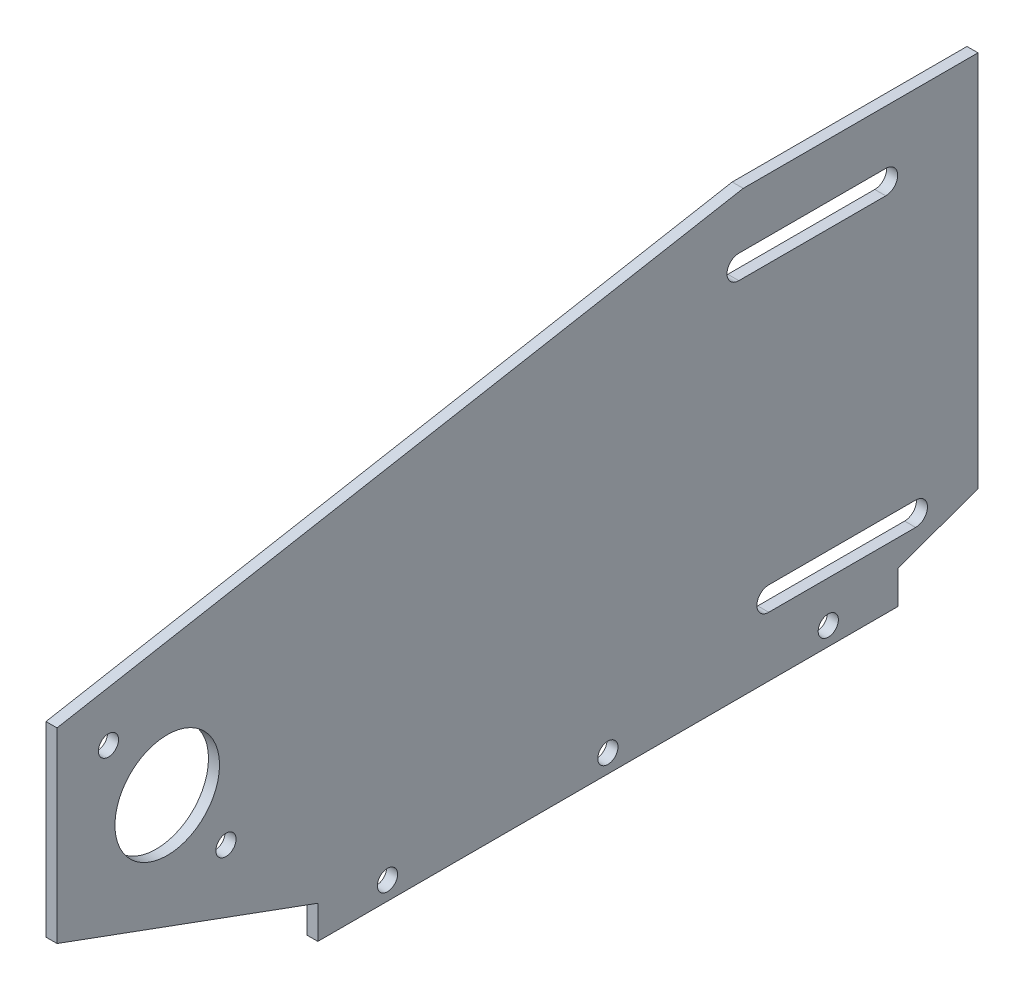
SolidWorks part; units mm, degrees
ref_plane "Front Plane" through (0, 0, 0) normal (0, 0, 1) x (1, 0, 0)
ref_plane "Top Plane" through (0, 0, 0) normal (0, 1, 0) x (1, 0, 0)
ref_plane "Right Plane" through (0, 0, 0) normal (1, 0, 0) x (0, 0, -1)
sketch "Sketch1" plane through (0, 0, 0) normal (1, 0, 0) x (0, 0, -1)
  line L1 (0, 0) -> (300, 0)
  line L2 (0, 0) -> (0, 150)
  line L3 (0, 150) -> (300, 150)
  line L4 (300, 0) -> (300, 150)
  circle A0 centre (30, 55) radius 14.235
  dimension "D1" = 300
  dimension "D5" = 28.47
  dimension "D4" = 55
  dimension "D2" = 150
  dimension "D3" = 30
extrude "Boss-Extrude1" add sketch "Sketch1" along normal blind 3
sketch "Sketch2" plane through (0, 0, 0) normal (-1, 0, 0) x (0, 0, 1)
  line L3 (-185.6114, 101.7084) -> (-225.6114, 101.7084) construction
  line L4 (-185.6114, 98.4784) -> (-225.6114, 98.4784)
  line L5 (-185.6114, 104.9384) -> (-225.6114, 104.9384)
  line L11 (-233.7436, 19.4567) -> (-193.7436, 19.4567) construction
  line L12 (-233.7436, 22.6817) -> (-193.7436, 22.6817)
  line L13 (-233.7436, 16.2317) -> (-193.7436, 16.2317)
  line L14 (0, 0) -> (-300, 0) construction
  line L15 (-300, 150) -> (0, 150) construction
  line L16 (-300, 0) -> (-300, 150) construction
  line L17 (0, 150) -> (0, 0) construction
  arc A3 (-185.6114, 98.4784) -> (-185.6114, 104.9384) centre (-185.6114, 101.7084) ccw
  arc A4 (-225.6114, 104.9384) -> (-225.6114, 98.4784) centre (-225.6114, 101.7084) ccw
  arc A9 (-233.7436, 22.6817) -> (-233.7436, 16.2317) centre (-233.7436, 19.4567) ccw
  arc A10 (-193.7436, 16.2317) -> (-193.7436, 22.6817) centre (-193.7436, 19.4567) ccw
  circle A11 centre (-290, 140) radius 3.225
  circle A12 centre (-10, 110) radius 3.225
  circle A13 centre (-290, 30) radius 3.225
  point P9 (-205.6114, 101.7084)
  point P34 (-213.7436, 19.4567)
  dimension "D8" = 3.225
  dimension "D13" = 6.45
  dimension "D14" = 6.45
  dimension "D15" = 6.45
  dimension "D3" = 40
  dimension "D5" = 40
  dimension "D16" = 10
  dimension "D17" = 10
  dimension "D18" = 30
  dimension "D19" = 10
  dimension "D20" = 10
  dimension "D21" = 110
extrude "Cut-Extrude1" cut sketch "Sketch2" against normal up to next
sketch "Sketch3" plane through (3, 0, 0) normal (1, 0, 0) x (0, 0, -1)
  line L0 (0, 150) -> (0, 0) construction
  line L1 (0, 0) -> (300, 0) construction
  circle A1 centre (14.0057, 74.7318) radius 2.75
  circle A2 centre (45.9943, 35.2682) radius 2.75
  dimension "D5" = 5.5
  dimension "D6" = 5.5
  dimension "D1" = 14.0057
  dimension "D2" = 45.9943
  dimension "D3" = 74.7318
  dimension "D4" = 35.2682
extrude "Cut-Extrude2" cut sketch "Sketch3" against normal through all
sketch "Sketch4" plane through (3, 0, 0) normal (1, 0, 0) x (0, 0, -1)
  line L0 (71, 9) -> (0, 35)
  line L1 (0, 150) -> (0, 0) construction
  line L2 (0, 35) -> (0, 0)
  line L3 (0, 0) -> (71, 0)
  line L4 (0, 0) -> (300, 0) construction
  line L5 (71, 9) -> (71, 0) construction
  line L6 (71, 0) -> (71, 9)
  dimension "D1" = 35
  dimension "D2" = 71
  dimension "D3" = 9
extrude "Cut-Extrude3" cut sketch "Sketch4" against normal through all
sketch "Sketch5" plane through (3, 0, 0) normal (1, 0, 0) x (0, 0, -1)
  line L0 (228.924, 9) -> (250.718, 16.8759)
  line L4 (71, 0) -> (300, 0) construction
  line L5 (228.924, 9) -> (228.924, 0) construction
  line L6 (228.924, 0) -> (228.924, 9)
  line L7 (250.718, 16.8759) -> (250.718, 150)
  line L8 (300, 150) -> (0, 150) construction
  line L9 (250.718, 150) -> (312.6604, 150)
  line L10 (312.6604, 150) -> (312.6604, -2.8296)
  line L11 (312.6604, -2.8296) -> (228.924, 0)
extrude "Cut-Extrude4" cut sketch "Sketch5" against normal blind 10
sketch "Sketch6" plane through (3, 0, 0) normal (1, 0, 0) x (0, 0, -1)
  line L0 (0, 85.8486) -> (186.8026, 119.6415)
  line L1 (0, 150) -> (0, 35) construction
  line L4 (0, 150) -> (0, 85.8486)
  line L6 (0, 150) -> (250.718, 150)
  line L8 (186.8026, 119.6415) -> (250.718, 119.6415)
  line L9 (250.718, 150) -> (250.718, 16.8759) construction
  line L10 (250.718, 119.6415) -> (250.718, 150)
extrude "Cut-Extrude5" cut sketch "Sketch6" against normal blind 10
sketch "Sketch7" plane through (0, 0, 0) normal (-1, 0, 0) x (0, 0, 1)
  line L0 (-71, 0) -> (-228.924, 0) construction
  circle A0 centre (-209.962, 5) radius 2.75
  circle A1 centre (-149.962, 5) radius 2.75
  circle A2 centre (-89.962, 5) radius 2.75
  point P8 (-149.962, 0)
  dimension "D1" = 5.5
  dimension "D2" = 5.5
  dimension "D3" = 5.5
  dimension "D4" = 60
  dimension "D5" = 60
  dimension "D6" = 5
extrude "Cut-Extrude6" cut sketch "Sketch7" against normal through all
